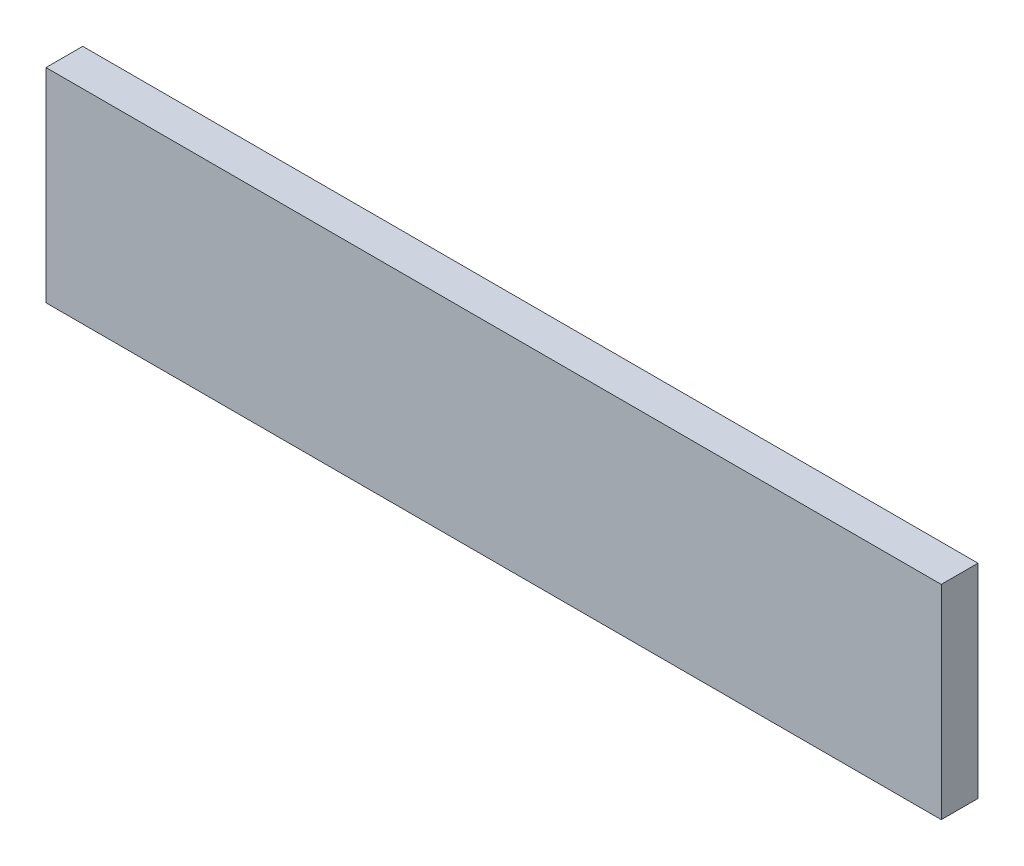
SolidWorks part; units mm, degrees
ref_plane "Ebene vorne" through (0, 0, 0) normal (0, 0, 1) x (1, 0, 0)
ref_plane "Ebene oben" through (0, 0, 0) normal (0, 1, 0) x (1, 0, 0)
ref_plane "Ebene rechts" through (0, 0, 0) normal (1, 0, 0) x (0, 0, -1)
sketch "Sketch1" plane through (0, 0, 0) normal (0, 0, 1) x (1, 0, 0)
  line L1 (-268, -75) -> (268, -75)
  line L2 (-268, -75) -> (-268, 75)
  line L3 (-268, 75) -> (268, 75)
  line L4 (268, -75) -> (268, 75)
  line L5 (-268, -75) -> (268, 75) construction
  line L6 (-268, 75) -> (268, -75) construction
  point P0 (0, 0)
  dimension "D1" = 536
  dimension "D2" = 150
extrude "Boss-Extrude1" add sketch "Sketch1" along normal blind 22
sketch "Sketch2" plane through (0, 0, 22) normal (0, 0, 1) x (1, 0, 0)
  line L0 (-268, 75) -> (-268, 47)
  line L1 (-268, 75) -> (-268, -75) construction
  line L3 (-268, 47) -> (268, 47)
  line L4 (-268, 47) -> (-268, 75)
  line L5 (-268, 75) -> (268, 75)
  line L6 (268, 47) -> (268, 75)
  line M2 (268, -75) -> (268, 75)
  line M3 (268, 75) -> (-268, 75)
  line M4 (-268, 75) -> (-268, -75)
  dimension "D1" = 28
extrude "Cut-Extrude1" cut sketch "Sketch2" against normal through all contours L3 M4 M2 M3
